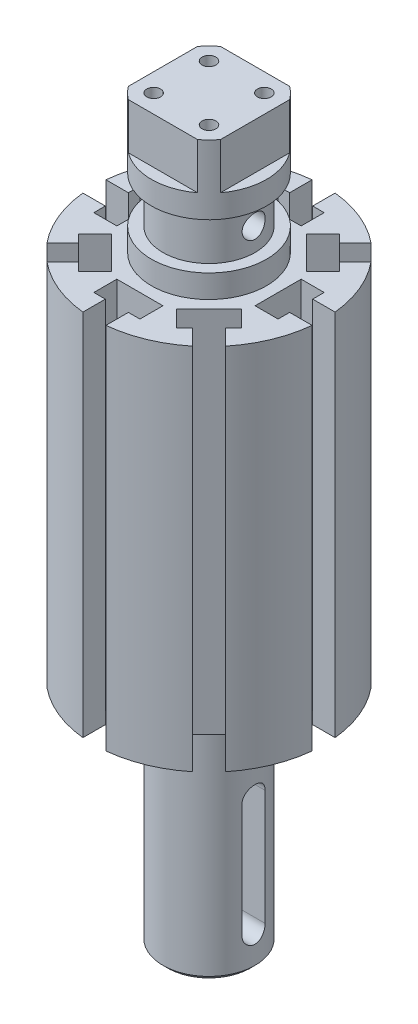
SolidWorks part; units mm, degrees
ref_plane "Front Plane" through (0, 0, 0) normal (0, 0, 1) x (1, 0, 0)
ref_plane "Top Plane" through (0, 0, 0) normal (0, 1, 0) x (1, 0, 0)
ref_plane "Right Plane" through (0, 0, 0) normal (1, 0, 0) x (0, 0, -1)
sketch "Sketch1" plane through (0, 0, 0) normal (0, 0, 1) x (1, 0, 0)
  line L0 (0, 0) -> (10, 0)
  line L1 (10, 0) -> (10, 50)
  line L2 (10, 50) -> (25, 50)
  line L3 (25, 50) -> (25, 130)
  line L4 (25, 130) -> (12.5, 130)
  line L5 (12.5, 130) -> (12.5, 135)
  line L6 (12.5, 135) -> (10, 135)
  line L7 (10, 135) -> (10, 145)
  line L8 (10, 145) -> (12.5, 145)
  line L9 (12.5, 145) -> (12.5, 160)
  line L11 (12.5, 160) -> (0, 160)
  line L13 (0, 0) -> (0, 160) construction
  line L14 (0, 0) -> (0, 160)
  dimension "D1" = 80
  dimension "D2" = 50
  dimension "D3" = 10
  dimension "D4" = 12.5
  dimension "D5" = 10
  dimension "D6" = 5
  dimension "D7" = 160
  dimension "D9" = 25
  dimension "D10" = 10
revolve "Revolve8" add sketch "Sketch1" angle 360 about L13
chamfer "Chamfer1" distance 1 angle 45 1 edges at (0, 0, -10)
sketch "Sketch2" plane through (0, 0, 0) normal (0, 1, 0) x (1, 0, 0)
  line L0 (24.8747, 2.5) -> (20, 2.5)
  line L1 (20, 2.5) -> (20, 5)
  line L2 (20, 5) -> (15, 5)
  line L3 (15, 5) -> (15, -5)
  line L4 (15, -5) -> (20, -5)
  line L5 (20, -5) -> (20, -2.5)
  line L6 (20, -2.5) -> (24.8747, -2.5)
  arc A0 (24.8747, -2.5) -> (24.8747, 2.5) centre (0, 0) ccw
  circle A1 centre (0, 0) radius 25 construction
  dimension "D1" = 10
  dimension "D2" = 5
  dimension "D3" = 5
  dimension "D4" = 2.5
  dimension "D5" = 15
  dimension "D6" = 20
extrude "Cut-Extrude6" cut sketch "Sketch2" along normal up to surface (130 mm away) up to face at (0, 130, -12.5)
pattern_circular "CirPattern1" count 8 over 360 about axis through (0, 0, 0) along (0, 1, 0) of "Cut-Extrude6"
ref_plane "Plane1" through (0, 160, 0) normal (0, 1, 0) x (1, 0, 0)
sketch "Sketch3" plane through (0, 160, 0) normal (0, 1, 0) x (1, 0, 0)
  line L1 (-7.5, 10) -> (7.5, 10)
  line L2 (-10, 7.5) -> (-10, -7.5)
  line L3 (-7.5, -10) -> (7.5, -10)
  line L4 (10, 7.5) -> (10, -7.5)
  arc A0 (-10, 7.5) -> (-10, -7.5) centre (0, 0) ccw
  circle A1 centre (0, 0) radius 12.5 construction
  arc A2 (-7.5, -10) -> (7.5, -10) centre (0, 0) ccw
  arc A3 (10, -7.5) -> (10, 7.5) centre (0, 0) ccw
  arc A4 (7.5, 10) -> (-7.5, 10) centre (0, 0) ccw
  dimension "D1" = 20
  dimension "D2" = 20
  dimension "D3" = 10
  dimension "D4" = 10
extrude "Cut-Extrude8" cut sketch "Sketch3" against normal blind 10
sketch "Sketch4" plane through (0, 160, 0) normal (0, 1, 0) x (1, 0, 0)
  circle A0 centre (-6, 6) radius 1.5
  circle A1 centre (6, 6) radius 1.5
  circle A2 centre (6, -6) radius 1.5
  circle A3 centre (-6, -6) radius 1.5
  dimension "D1" = 3
  dimension "D2" = 12
  dimension "D3" = 6
  dimension "D4" = 12
  dimension "D5" = 6
extrude "Cut-Extrude9" cut sketch "Sketch4" against normal blind 15
sketch "Sketch5" plane through (-10, 0, 0) normal (-1, 0, 0) x (0, 0, 1)
  line L0 (-2.5, 130) -> (-15.8213, 130) construction
  circle A0 centre (0, 140) radius 2.5
  dimension "D1" = 5
  dimension "D2" = 10
extrude "Cut-Extrude10" cut sketch "Sketch5" against normal blind 20
sketch "Sketch6" plane through (-10, 0, 0) normal (-1, 0, 0) x (0, 0, 1)
  line L0 (0, 32.5) -> (0, 7.5) construction
  line L1 (2.5, 32.5) -> (2.5, 7.5)
  line L2 (-2.5, 32.5) -> (-2.5, 7.5)
  arc A0 (2.5, 32.5) -> (-2.5, 32.5) centre (0, 32.5) ccw
  arc A1 (-2.5, 7.5) -> (2.5, 7.5) centre (0, 7.5) ccw
  point P3 (0, 20)
  dimension "D1" = 25
  dimension "D2" = 5
  dimension "D3" = 7.5
extrude "Cut-Extrude11" cut sketch "Sketch6" against normal blind 20
